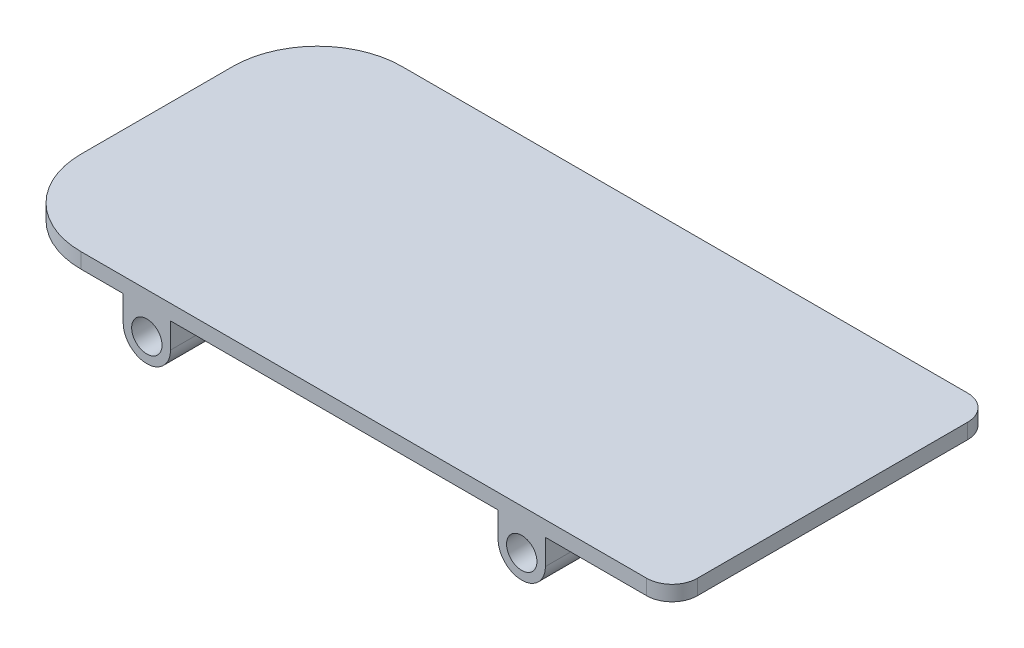
SolidWorks part; units mm, degrees
ref_plane "Ön Düzlem" through (0, 0, 0) normal (0, 0, 1) x (1, 0, 0)
ref_plane "Üst Düzlem" through (0, 0, 0) normal (0, 1, 0) x (1, 0, 0)
ref_plane "Sağ Düzlem" through (0, 0, 0) normal (1, 0, 0) x (0, 0, -1)
sketch "Çizim1" plane through (0, 0, 0) normal (0, 0, 1) x (1, 0, 0)
  line L0 (-28, 0) -> (-28, 30)
  line L1 (622, 30) -> (622, 48)
  line L2 (28, 30) -> (28, 0)
  line L3 (-28, 30) -> (-178, 30)
  line L4 (-178, 30) -> (-178, 48)
  line L5 (-178, 48) -> (622, 48)
  line L7 (416, 30) -> (28, 30)
  line L8 (472, 30) -> (622, 30)
  line L9 (416, 30) -> (416, 0)
  line L10 (472, 0) -> (472, 30)
  arc A0 (-28, 0) -> (28, 0) centre (0, 0) ccw
  circle A1 centre (0, 0) radius 18
  circle A2 centre (444, 0) radius 18
  arc A3 (472, 0) -> (416, 0) centre (444, 0) cw
  dimension "D1" = 56
  dimension "D6" = 36
  dimension "D2" = 30
  dimension "D3" = 18
  dimension "D4" = 150
extrude "Yükseklik-Ekstrüzyon1" add sketch "Çizim1" along normal blind 380
fillet "Radyus1" radius 100 2 edges at (-178, 39, 0) (-178, 39, 380)
fillet "Radyus2" radius 30 2 edges at (622, 39, 380) (622, 39, 0)
